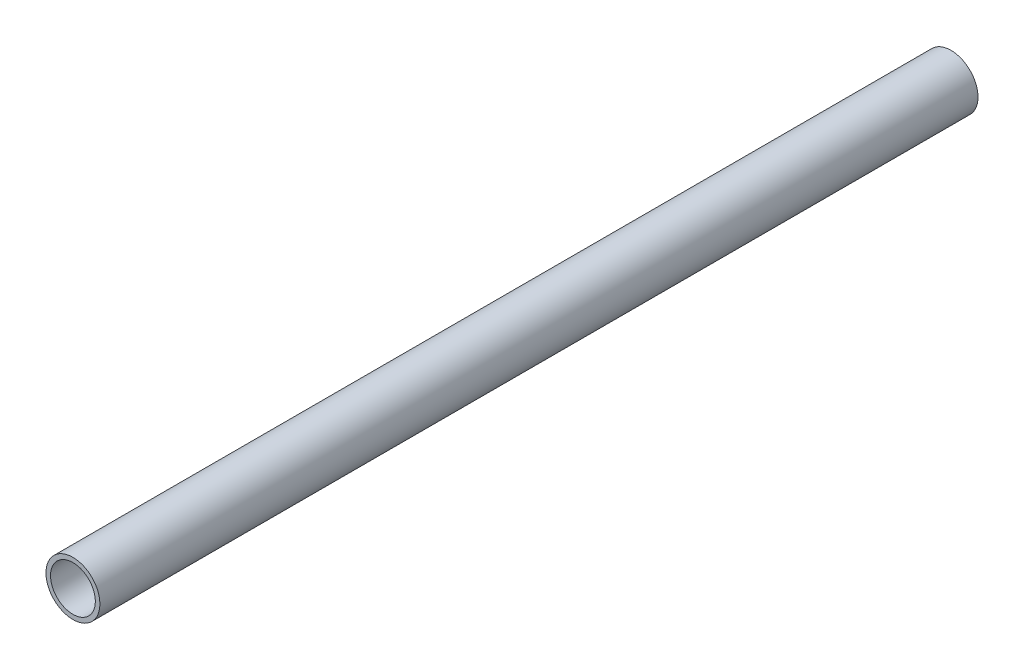
SolidWorks part; units mm, degrees
material "Plain Carbon Steel"
ref_plane "Front Plane" through (0, 0, 0) normal (0, 0, 1) x (1, 0, 0)
ref_plane "Top Plane" through (0, 0, 0) normal (0, 1, 0) x (1, 0, 0)
ref_plane "Right Plane" through (0, 0, 0) normal (1, 0, 0) x (0, 0, -1)
sketch "Sketch1" plane through (0, 0, 0) normal (0, 0, 1) x (1, 0, 0)
  circle A0 centre (164.3062, 199.9864) radius 21.082
  circle A1 centre (164.3062, 199.9864) radius 17.526
  circle A3 centre (164.3062, 199.9864) radius 21.082 construction
  dimension "D1" = 42.164
  dimension "D2" = 35.052
extrude "Boss-Extrude1" add sketch "Sketch1" against normal up to surface (686.3558 mm away)
